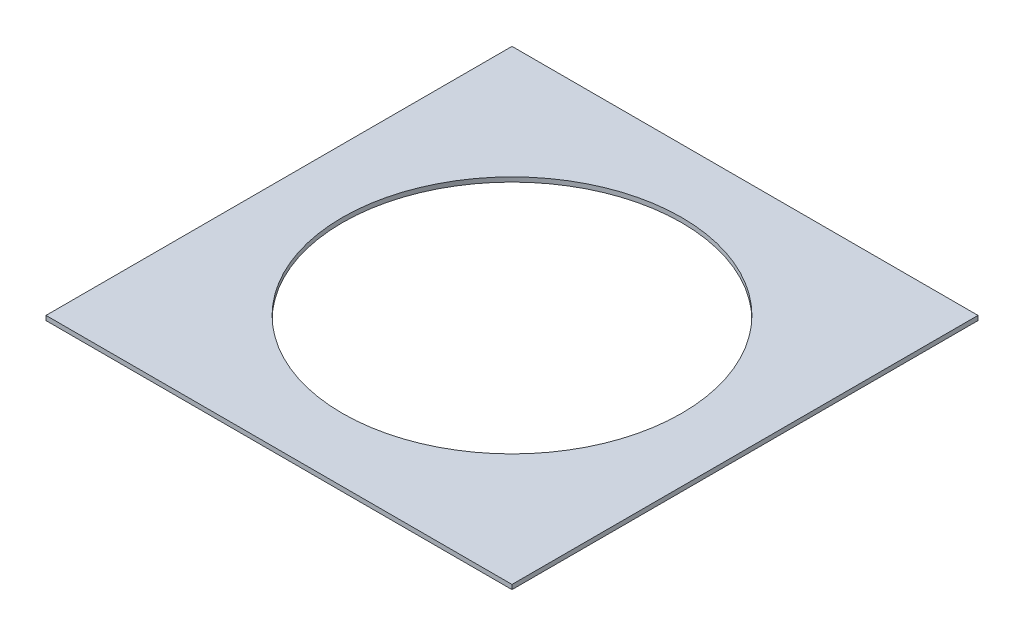
SolidWorks part; units mm, degrees
ref_plane "Front Plane" through (0, 0, 0) normal (0, 0, 1) x (1, 0, 0)
ref_plane "Top Plane" through (0, 0, 0) normal (0, 1, 0) x (1, 0, 0)
ref_plane "Right Plane" through (0, 0, 0) normal (1, 0, 0) x (0, 0, -1)
sketch "Sketch1" plane through (0, 0, 0) normal (0, 1, 0) x (1, 0, 0)
  line L1 (-103, 103) -> (103, 103)
  line L2 (-103, 103) -> (-103, -103)
  line L3 (-103, -103) -> (103, -103)
  line L4 (103, 103) -> (103, -103)
  line L5 (-103, 103) -> (103, -103) construction
  line L6 (-103, -103) -> (103, 103) construction
  circle A0 centre (0, 0) radius 75
  dimension "D2" = 150
  dimension "D1" = 206
extrude "Boss-Extrude1" add sketch "Sketch1" along normal blind 2
